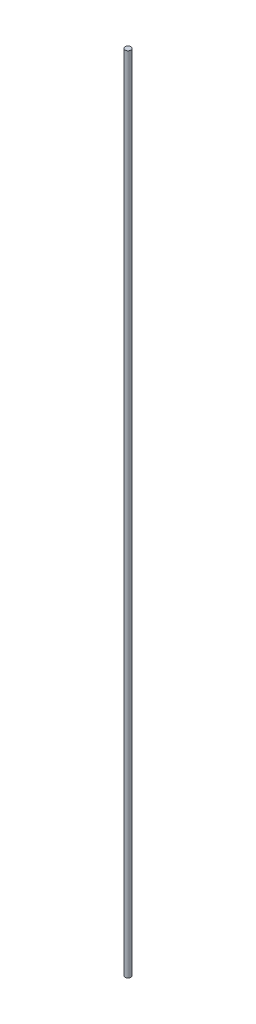
SolidWorks part; units mm, degrees
ref_plane "Спереди" through (0, 0, 0) normal (0, 0, 1) x (1, 0, 0)
ref_plane "Сверху" through (0, 0, 0) normal (0, 1, 0) x (1, 0, 0)
ref_plane "Справа" through (0, 0, 0) normal (1, 0, 0) x (0, 0, -1)
sketch "Эскиз1" plane through (0, 0, 0) normal (0, 1, 0) x (1, 0, 0)
  circle A0 centre (0, 0) radius 4
  dimension "D1" = 8
extrude "Бобышка-Вытянуть1" add sketch "Эскиз1" along normal blind 1092.5
